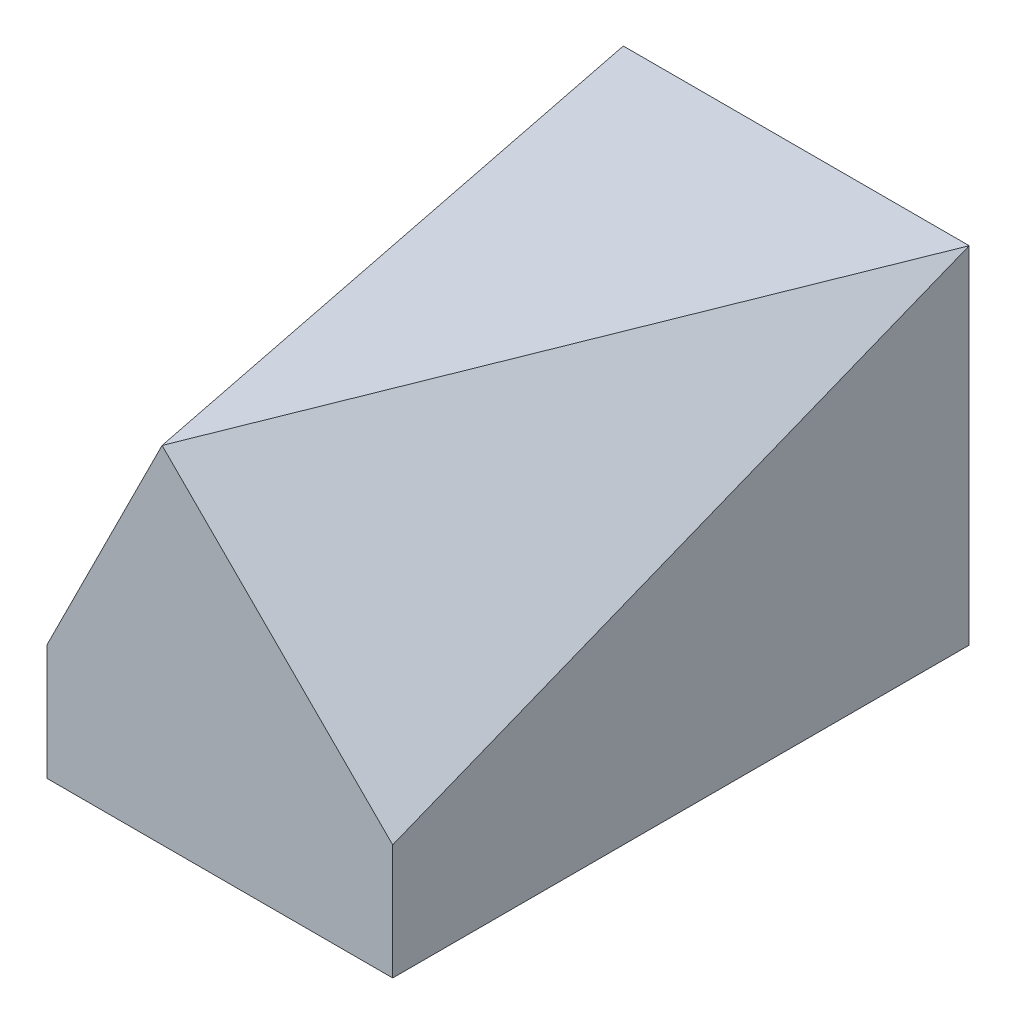
SolidWorks part; units mm, degrees
ref_plane "前基準面" through (0, 0, 0) normal (0, 0, 1) x (1, 0, 0)
ref_plane "上基準面" through (0, 0, 0) normal (0, 1, 0) x (1, 0, 0)
ref_plane "右基準面" through (0, 0, 0) normal (1, 0, 0) x (0, 0, -1)
sketch "草圖1" plane through (0, 0, 0) normal (0, 1, 0) x (1, 0, 0)
  line L1 (-7.5, -12.5) -> (7.5, -12.5)
  line L2 (-7.5, -12.5) -> (-7.5, 12.5)
  line L3 (-7.5, 12.5) -> (7.5, 12.5)
  line L4 (7.5, -12.5) -> (7.5, 12.5)
  line L5 (-7.5, -12.5) -> (7.5, 12.5) construction
  line L6 (-7.5, 12.5) -> (7.5, -12.5) construction
  point P0 (0, 0)
  dimension "D1" = 25
  dimension "D2" = 15
extrude "填料-伸長1" add sketch "草圖1" along normal blind 15
sketch "草圖2" plane through (0, 0, 12.5) normal (0, 0, 1) x (1, 0, 0)
  line L0 (-2.5, 15) -> (-7.5, 5)
  line L1 (-7.5, 15) -> (7.5, 15) construction
  line L2 (-7.5, 15) -> (-7.5, 0) construction
  line L3 (-2.5, 15) -> (7.5, 5)
  line L4 (7.5, 15) -> (7.5, 0) construction
  dimension "D1" = 10
  dimension "D2" = 5
sketch "草圖3" plane through (0, 15, 0) normal (0, 1, 0) x (1, 0, 0)
  line L0 (-2.5, -12.5) -> (-7.5, 12.5)
  line L1 (-2.5, -12.5) -> (7.5, -12.5) construction
  line L2 (-2.5, -12.5) -> (7.5, 12.5)
  line L3 (7.5, 12.5) -> (-7.5, 12.5) construction
  line L4 (7.5, -12.5) -> (7.5, 12.5) construction
  dimension "D1" = 5
ref_plane "平面1" through (-9.6899, 4.845, 1.938) normal (-0.8805, 0.4402, 0.1761) x (0.1575, -0.0787, 0.9844)
sketch "草圖4" plane through (-9.6899, 4.845, 1.938) normal (-0.8805, 0.4402, 0.1761) x (0.1575, -0.0787, 0.9844)
  line L1 (-15.1637, 18.6746) -> (18.2966, 18.6746)
  line L2 (-15.1637, 18.6746) -> (-15.1637, -8.0133)
  line L3 (-15.1637, -8.0133) -> (18.2966, -8.0133)
  line L4 (18.2966, 18.6746) -> (18.2966, -8.0133)
extrude "除料-伸長1" cut sketch "草圖4" along normal blind 15
ref_plane "平面2" through (8.1019, 8.1019, 3.2407) normal (-0.6804, -0.6804, -0.2722) x (-0.1925, -0.1925, 0.9623)
sketch "草圖5" plane through (8.1019, 8.1019, 3.2407) normal (-0.6804, -0.6804, -0.2722) x (-0.1925, -0.1925, 0.9623)
  line L1 (18.6645, 17.0838) -> (-22.3565, 17.0838)
  line L2 (18.6645, 17.0838) -> (18.6645, -6.1521)
  line L3 (18.6645, -6.1521) -> (-22.3565, -6.1521)
  line L4 (-22.3565, 17.0838) -> (-22.3565, -6.1521)
extrude "除料-伸長2" cut sketch "草圖5" against normal blind 15
scale "縮放比例1" scale about centroid uniform scaling yes scale factor 0.2
